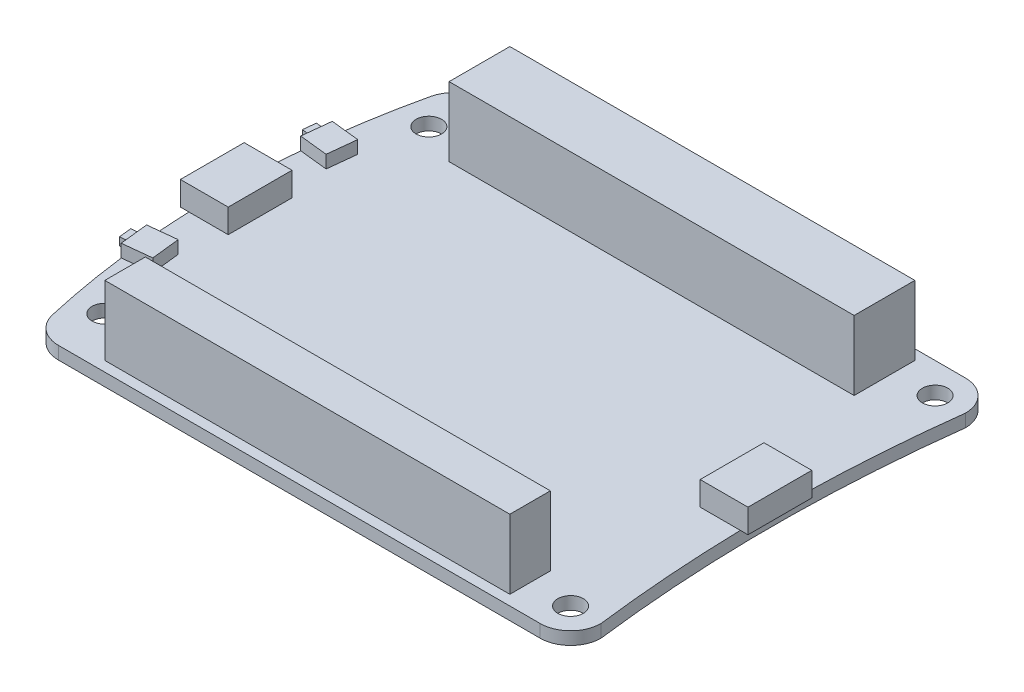
SolidWorks part; units mm, degrees
ref_plane "Front Plane" through (0, 0, 0) normal (0, 0, 1) x (1, 0, 0)
ref_plane "Top Plane" through (0, 0, 0) normal (0, 1, 0) x (1, 0, 0)
ref_plane "Right Plane" through (0, 0, 0) normal (1, 0, 0) x (0, 0, -1)
sketch "Sketch1" plane through (0, 0, 0) normal (0, 1, 0) x (1, 0, 0)
  line L0 (0, 20.2635) -> (0, -20.6983) construction
  line L1 (-48.5386, 0) -> (50.9036, 0) construction
  line L2 (-36.322, 3.1321) -> (-36.322, 0) construction
  line L3 (30.48, 26.67) -> (-38.692, 26.67) construction
  line L4 (32.868, 0.8812) -> (32.868, 0) construction
  line L5 (30.48, 26.67) -> (-29.9413, 26.67)
  line L6 (30.48, -26.67) -> (-29.9413, -26.67)
  circle A0 centre (30.48, 22.86) radius 1.6
  circle A1 centre (30.48, 22.86) radius 3.81 construction
  circle A2 centre (-30.48, 20.32) radius 1.6
  circle A3 centre (-30.48, 20.32) radius 3.81 construction
  arc A4 (34.29, -22.86) -> (34.29, 22.86) centre (217.3271, 0) cw
  arc A5 (-33.6457, -23.7168) -> (-33.6457, 23.7168) centre (70.104, 0) cw
  arc A6 (-33.6457, 23.7168) -> (-29.9413, 26.67) centre (-29.9413, 22.87) cw
  arc A7 (30.48, 26.67) -> (34.29, 22.86) centre (30.48, 22.86) cw
  circle A8 centre (30.48, -22.86) radius 1.6
  arc A9 (30.48, -26.67) -> (34.29, -22.86) centre (30.48, -22.86) ccw
  circle A10 centre (30.48, -22.86) radius 3.81 construction
  circle A11 centre (-30.48, -20.32) radius 3.81 construction
  circle A12 centre (-30.48, -20.32) radius 1.6
  arc A13 (-33.6457, -23.7168) -> (-29.9413, -26.67) centre (-29.9413, -22.87) ccw
  point P21 (-32.9261, 26.67)
  dimension "D1" = 3.2
  dimension "D4" = 7.62
  dimension "D6" = 3.2
  dimension "D8" = 7.62
  dimension "D11" = 3.8
  dimension "D2" = 22.86
  dimension "D3" = 30.48
  dimension "D5" = 30.48
  dimension "D7" = 40.64
  dimension "D9" = 2.388
  dimension "D10" = 70.612
extrude "Boss-Extrude1" add sketch "Sketch1" along normal blind 1.6
sketch "Sketch2" plane through (0, 1.6, 0) normal (0, 1, 0) x (1, 0, 0)
  line L0 (-48.3558, 0) -> (44.4902, 0) construction
  line L1 (-37.322, 4) -> (-31.322, 4)
  line L2 (-37.322, 4) -> (-37.322, -4)
  line L3 (-37.322, -4) -> (-31.322, -4)
  line L4 (-31.322, 4) -> (-31.322, -4)
  line L5 (-37.322, 4) -> (-31.322, -4) construction
  line L6 (-37.322, -4) -> (-31.322, 4) construction
  line L7 (27.868, 4) -> (33.868, 4)
  line L8 (27.868, 4) -> (27.868, -4)
  line L9 (27.868, -4) -> (33.868, -4)
  line L10 (33.868, 4) -> (33.868, -4)
  line L11 (27.868, 4) -> (33.868, -4) construction
  line L12 (27.868, -4) -> (33.868, 4) construction
  line L13 (-36.322, 6.3556) -> (-36.322, -6.7058) construction
  line L14 (32.868, 2.2455) -> (32.868, -2.9301) construction
  arc A2 (-33.6457, 23.7168) -> (-33.6457, -23.7168) centre (70.104, 0) ccw construction
  arc A3 (34.29, 22.86) -> (34.29, -22.86) centre (217.3271, 0) ccw construction
  point P0 (-34.322, 0)
  point P5 (30.868, 0)
  dimension "D1" = 8
  dimension "D2" = 6
  dimension "D3" = 6
  dimension "D4" = 8
  dimension "D5" = 1
  dimension "D6" = 1
extrude "Boss-Extrude2" add sketch "Sketch2" along normal blind 3
sketch "Sketch3" plane through (0, 1.6, 0) normal (0, 1, 0) x (1, 0, 0)
  line L0 (-41.7712, 0) -> (43.4289, 0) construction
  line L1 (-42.2343, 11.45) -> (-29.091, 11.45) construction
  line L2 (-34.4806, 22.7576) -> (-35.7043, 11.45) construction
  line L3 (-35.7043, 11.45) -> (-16.5909, 9.3817) construction
  line L4 (-35.5106, 13.2396) -> (-31.9315, 12.8522)
  line L5 (-35.5106, 13.2396) -> (-35.8979, 9.6604)
  line L6 (-31.9315, 12.8522) -> (-32.3188, 9.2731)
  line L7 (-35.8979, 9.6604) -> (-32.3188, 9.2731)
  line L8 (-31.9315, -12.8522) -> (-32.3188, -9.2731)
  line L9 (-35.8979, -9.6604) -> (-32.3188, -9.2731)
  line L10 (-35.5106, -13.2396) -> (-35.8979, -9.6604)
  line L11 (-35.5106, -13.2396) -> (-31.9315, -12.8522)
  arc A0 (-33.6457, 23.7168) -> (-36.2468, 4) centre (70.104, 0) ccw construction
  dimension "D1" = 11.45
  dimension "D2" = 3.6
  dimension "D3" = 1.8
  dimension "D4" = 3.6
extrude "Boss-Extrude3" add sketch "Sketch3" along normal blind 1.6
sketch "Sketch4" plane through (-36.5157, 0, 3.9515) normal (-0.9942, 0, 0.1076) x (0.1076, 0, 0.9942)
  line L8 (5.7422, 3.2) -> (5.7422, 1.6) construction
  line L9 (6.7422, 1.9) -> (8.3422, 1.9)
  line L10 (6.7422, 1.9) -> (6.7422, 2.9)
  line L11 (6.7422, 2.9) -> (8.3422, 2.9)
  line L12 (8.3422, 1.9) -> (8.3422, 2.9)
  line L13 (6.7422, 1.9) -> (8.3422, 2.9) construction
  line L14 (6.7422, 2.9) -> (8.3422, 1.9) construction
  line L15 (9.3422, 3.2) -> (9.3422, 1.6) construction
  line L16 (5.7422, 3.2) -> (9.3422, 3.2) construction
  line L17 (7.5422, 1.6) -> (9.3422, 1.6) construction
  point P0 (7.5422, 2.4)
  dimension "D1" = 1
  dimension "D2" = 1
  dimension "D3" = 0.3
  dimension "D4" = 0.3
extrude "Boss-Extrude4" add sketch "Sketch4" along normal blind 1
sketch "Sketch5" plane through (-36.5157, 0, -3.9515) normal (-0.9942, 0, -0.1076) x (-0.1076, 0, 0.9942)
  line L0 (-9.3422, 3.2) -> (-9.3422, 1.6) construction
  line L1 (-8.3422, 1.9) -> (-6.7422, 1.9)
  line L2 (-8.3422, 1.9) -> (-8.3422, 2.9)
  line L3 (-8.3422, 2.9) -> (-6.7422, 2.9)
  line L4 (-6.7422, 1.9) -> (-6.7422, 2.9)
  line L5 (-8.3422, 1.9) -> (-6.7422, 2.9) construction
  line L6 (-8.3422, 2.9) -> (-6.7422, 1.9) construction
  line L7 (-5.7422, 3.2) -> (-5.7422, 1.6) construction
  line L8 (-9.3422, 3.2) -> (-5.7422, 3.2) construction
  line L9 (-7.5422, 1.6) -> (-5.7422, 1.6) construction
  point P0 (-7.5422, 2.4)
  dimension "D1" = 1
  dimension "D2" = 1
  dimension "D3" = 0.3
  dimension "D4" = 0.3
extrude "Boss-Extrude5" add sketch "Sketch5" along normal blind 1
sketch "Sketch6" plane through (0, 1.6, 0) normal (0, 1, 0) x (1, 0, 0)
  line L0 (-29.9413, -26.67) -> (30.48, -26.67) construction
  line L1 (-25.4, -20.32) -> (25.4, -20.32)
  line L2 (-25.4, -20.32) -> (-25.4, -25.4)
  line L3 (-25.4, -25.4) -> (25.4, -25.4)
  line L4 (25.4, -20.32) -> (25.4, -25.4)
  line L5 (30.48, 26.67) -> (-29.9413, 26.67) construction
  line L6 (-25.4, 25.4) -> (25.4, 25.4)
  line L7 (-25.4, 25.4) -> (-25.4, 17.78)
  line L8 (-25.4, 17.78) -> (25.4, 17.78)
  line L9 (25.4, 25.4) -> (25.4, 17.78)
  dimension "D1" = 5.08
  dimension "D2" = 50.8
  dimension "D3" = 8.89
  dimension "D4" = 1.27
  dimension "D5" = 50.8
  dimension "D6" = 7.62
  dimension "D7" = 1.27
extrude "Boss-Extrude6" add sketch "Sketch6" along normal blind 8.7
